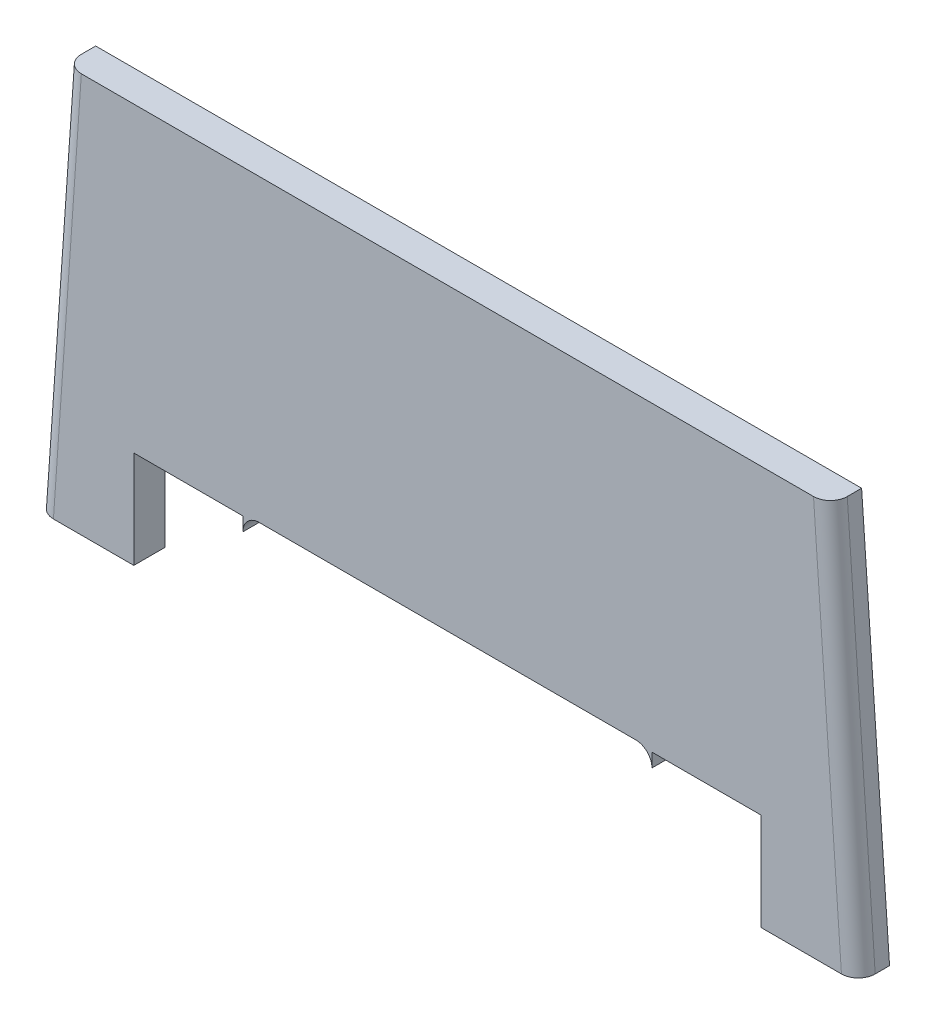
SolidWorks part; units mm, degrees
ref_plane "Front Plane" through (0, 0, 0) normal (0, 0, 1) x (1, 0, 0)
ref_plane "Top Plane" through (0, 0, 0) normal (0, 1, 0) x (1, 0, 0)
ref_plane "Right Plane" through (0, 0, 0) normal (1, 0, 0) x (0, 0, -1)
sketch "Sketch1" plane through (0, 0, 0) normal (0, 0, 1) x (1, 0, 0)
  line L1 (-251.2, -2) -> (-251.2, -80)
  line L2 (-251.2, -80) -> (-329.1, -80)
  line L3 (-329.1, -80) -> (-306.7234, 240)
  line L4 (-306.7234, 240) -> (306.7234, 240)
  line L5 (0, 240) -> (0, 0) construction
  line L6 (329.1, -80) -> (306.7234, 240)
  line L7 (251.2, -80) -> (329.1, -80)
  line L8 (251.2, -2) -> (251.2, -80)
  line L9 (-163.8, -2) -> (-163.8, -13)
  line L10 (-150.8, 0) -> (150.8, 0)
  line L12 (-163.8, -2) -> (-251.2, -2)
  line L13 (163.8, -2) -> (163.8, -13)
  line L14 (163.8, -2) -> (251.2, -2)
  arc A0 (-163.8, -13) -> (-150.8, 0) centre (-150.8, -13) cw
  arc A1 (163.8, -13) -> (150.8, 0) centre (150.8, -13) ccw
  point P19 (0, 0)
  dimension "D6" = 80
  dimension "D7" = 87.4
  dimension "D8" = 13
  dimension "D1" = 86
  dimension "D2" = 320
  dimension "D3" = 251.2
  dimension "D4" = 329.1
  dimension "D5" = 78
extrude "Boss-Extrude1" add sketch "Sketch1" along normal blind 25 contours L3 L4 L6 L7 L8 L14 L13 A1 L10 A0 L9 L12 L1 L2
fillet "Fillet1" radius 13.5 2 edges at (317.9117, 80, 25) (-317.9117, 80, 25)
